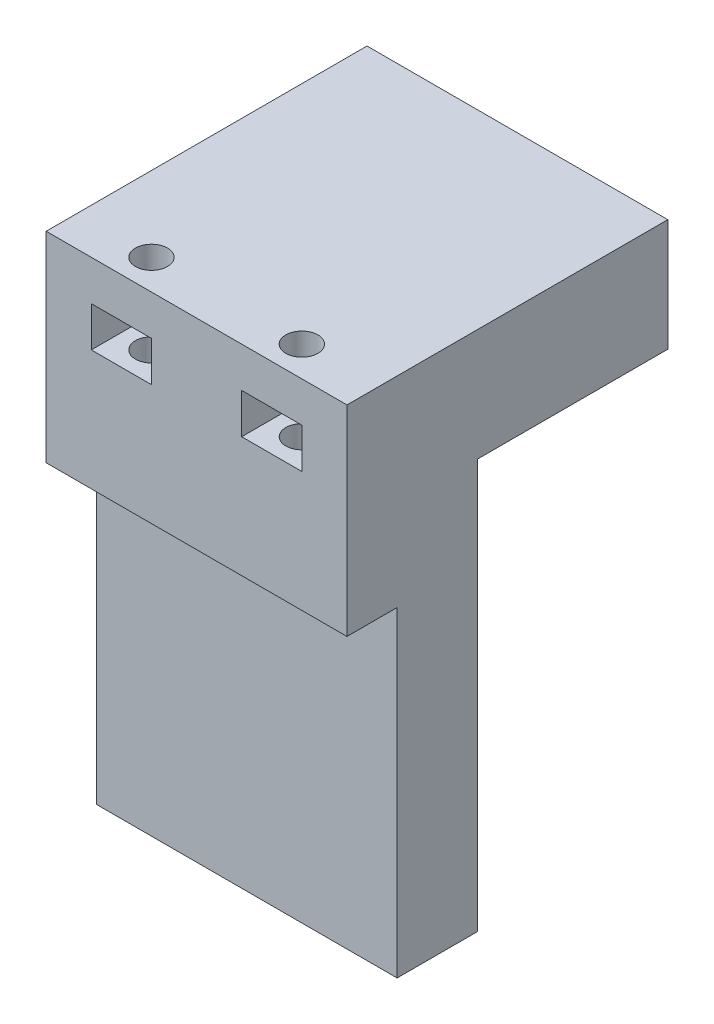
SolidWorks part; units mm, degrees
ref_plane "前视基准面" through (0, 0, 0) normal (0, 0, 1) x (1, 0, 0)
ref_plane "上视基准面" through (0, 0, 0) normal (0, 1, 0) x (1, 0, 0)
ref_plane "右视基准面" through (0, 0, 0) normal (1, 0, 0) x (0, 0, -1)
sketch "草图1" plane through (0, 0, 0) normal (0, 0, 1) x (1, 0, 0)
  line L0 (0, 14.6971) -> (0, -37.3029)
  line L1 (15, 3.5071) -> (-15, 3.5071)
  line L2 (15, 14.6971) -> (-15, 14.6971)
  line L3 (-15, 14.6971) -> (-15, -37.3029)
  line L4 (-15, -37.3029) -> (15, -37.3029)
  line L5 (15, -37.3029) -> (15, 14.6971)
  line L6 (-10, 3.5071) -> (10, 3.5071)
  line L7 (-10, 3.5071) -> (-10, -37.3029)
  line L8 (-10, -37.3029) -> (10, -37.3029)
  line L9 (-15, 14.6971) -> (-27.0802, 14.6971)
  line L10 (10, -37.3029) -> (10, 3.5071)
  point P6 (0, 3.5071)
  point P14 (0, 3.5071)
  dimension "D1" = 52
  dimension "D2" = 11.19
  dimension "D3" = 30
  dimension "D4" = 20
sketch "草图2" plane through (0, 0, 0) normal (0, 0, 1) x (1, 0, 0)
  line L1 (15, 14.6971) -> (-15, 14.6971)
  line L2 (15, 14.6971) -> (15, -37.3029)
  line L3 (15, -37.3029) -> (-15, -37.3029)
  line L4 (-15, 14.6971) -> (-15, -37.3029)
extrude "凸台-拉伸1" add sketch "草图2" along normal blind 5
sketch "草图3" plane through (0, 0, 0) normal (0, 0, 1) x (1, 0, 0)
  line L1 (-15, 3.5071) -> (-10, 3.5071)
  line L2 (-15, 3.5071) -> (-15, -37.3029)
  line L3 (-15, -37.3029) -> (-10, -37.3029)
  line L4 (-10, 3.5071) -> (-10, -37.3029)
  line L5 (10, 3.5071) -> (15, 3.5071)
  line L6 (10, 3.5071) -> (10, -37.3029)
  line L7 (10, -37.3029) -> (15, -37.3029)
  line L8 (15, 3.5071) -> (15, -37.3029)
extrude "凸台-拉伸2" add sketch "草图3" against normal blind 3
ref_plane "基准面1" through (0, 14.6971, 0) normal (0, 1, 0) x (1, 0, 0)
sketch "草图4" plane through (0, 14.6971, 0) normal (0, 1, 0) x (1, 0, 0)
  line L1 (-15, 0) -> (15, 0)
  line L2 (-15, 0) -> (-15, -10)
  line L3 (-15, -10) -> (15, -10)
  line L4 (15, 0) -> (15, -10)
  dimension "D1" = 10
  dimension "D2" = 30
extrude "凸台-拉伸3" add sketch "草图4" against normal blind 20
sketch "草图6" plane through (0, 14.6971, 0) normal (0, 1, 0) x (1, 0, 0)
  circle A0 centre (-7.5, -7) radius 1.6
  circle A1 centre (7.5, -7) radius 1.6
  point P3 (0, -7)
  dimension "D3" = 3.2
  dimension "D4" = 3.2
  dimension "D1" = 7
  dimension "D2" = 15
extrude "切除-拉伸1" cut sketch "草图6" against normal blind 15
ref_plane "基准面2" through (0, 0, 10) normal (0, 0, 1) x (1, 0, 0)
sketch "草图7" plane through (0, 0, 10) normal (0, 0, 1) x (1, 0, 0)
  line L3 (-10.5, 10.6971) -> (-4.5, 10.6971)
  line L4 (-10.5, 10.6971) -> (-10.5, 6.6971)
  line L5 (-10.5, 6.6971) -> (-4.5, 6.6971)
  line L6 (-4.5, 10.6971) -> (-4.5, 6.6971)
  line L7 (-10.5, 10.6971) -> (-4.5, 6.6971) construction
  line L8 (-10.5, 6.6971) -> (-4.5, 10.6971) construction
  line L9 (4.5, 10.6971) -> (10.5, 10.6971)
  line L10 (4.5, 10.6971) -> (4.5, 6.6971)
  line L11 (4.5, 6.6971) -> (10.5, 6.6971)
  line L12 (10.5, 10.6971) -> (10.5, 6.6971)
  line L13 (4.5, 10.6971) -> (10.5, 6.6971) construction
  line L14 (4.5, 6.6971) -> (10.5, 10.6971) construction
  point P3 (0, 8.6971)
  dimension "D1" = 6
  dimension "D3" = 4
  dimension "D4" = 4
  dimension "D5" = 6
  dimension "D6" = 6
extrude "切除-拉伸2" cut sketch "草图7" against normal blind 6
sketch "草图8" plane through (0, 0, 0) normal (0, 0, 1) x (1, 0, 0)
  line L1 (15, 14.6971) -> (-15, 14.6971)
  line L2 (15, 14.6971) -> (15, 3.5071)
  line L3 (15, 3.5071) -> (-15, 3.5071)
  line L4 (-15, 14.6971) -> (-15, 3.5071)
extrude "凸台-拉伸4" add sketch "草图8" against normal blind 22
ref_plane "基准面3" through (0, 0, -22) normal (0, 0, -1) x (-1, 0, 0)
sketch "草图9" plane through (0, 0, -22) normal (0, 0, -1) x (-1, 0, 0)
  line L2 (0, 14.6971) -> (0, -37.3029) construction
  line L3 (15, 3.5071) -> (-15, 3.5071) construction
  circle A0 centre (-5, 7.5071) radius 2.5
  circle A1 centre (5, 7.5071) radius 2.5
  point P3 (0, 7.5071)
  dimension "D3" = 5
  dimension "D4" = 5
  dimension "D1" = 10
  dimension "D2" = 4
extrude "切除-拉伸3" cut sketch "草图9" against normal blind 10
ref_plane "基准面4" through (0, 3.5071, 0) normal (0, -1, 0) x (-1, 0, 0)
sketch "草图10" plane through (0, 3.5071, 0) normal (0, -1, 0) x (-1, 0, 0)
  line L1 (6.1545, 22) -> (-6.1545, 22) construction
  line L3 (2, 18.75) -> (8, 18.75)
  line L4 (2, 18.75) -> (2, 15.25)
  line L5 (2, 15.25) -> (8, 15.25)
  line L6 (8, 18.75) -> (8, 15.25)
  line L7 (2, 18.75) -> (8, 15.25) construction
  line L8 (2, 15.25) -> (8, 18.75) construction
  line L9 (-8, 18.75) -> (-2, 18.75)
  line L10 (-8, 18.75) -> (-8, 15.25)
  line L11 (-8, 15.25) -> (-2, 15.25)
  line L12 (-2, 18.75) -> (-2, 15.25)
  line L13 (-8, 18.75) -> (-2, 15.25) construction
  line L14 (-8, 15.25) -> (-2, 18.75) construction
  point P3 (0, 17)
  dimension "D2" = 5
  dimension "D3" = 6
  dimension "D4" = 6
  dimension "D5" = 3.5
  dimension "D6" = 3.5
extrude "切除-拉伸4" cut sketch "草图10" against normal blind 8
